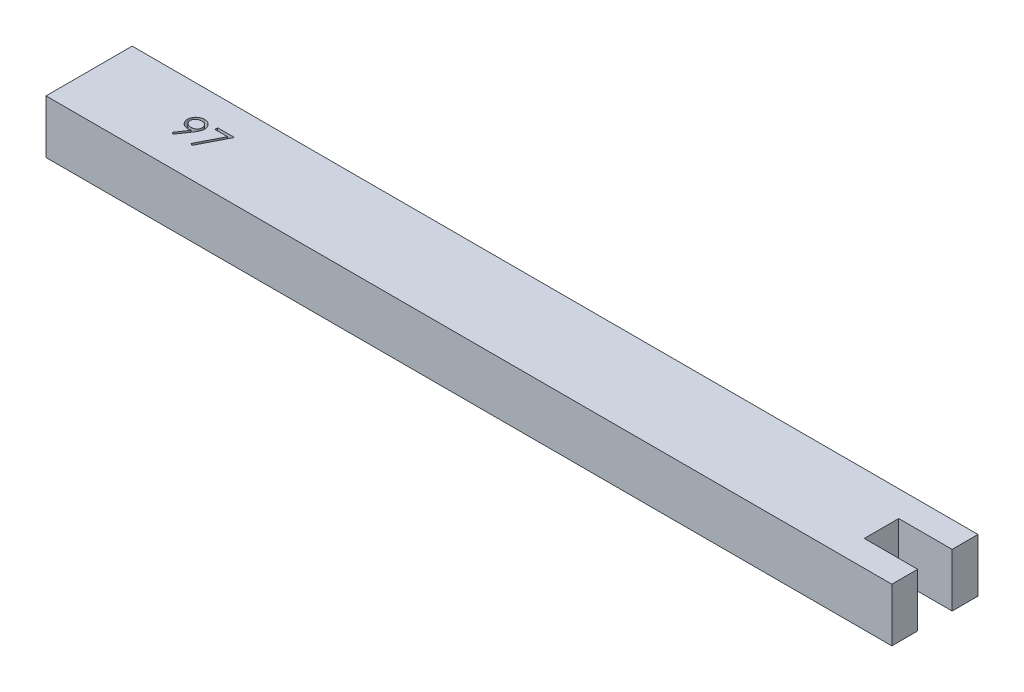
SolidWorks part; units mm, degrees
ref_plane "Front Plane" through (0, 0, 0) normal (0, 0, 1) x (1, 0, 0)
ref_plane "Top Plane" through (0, 0, 0) normal (0, 1, 0) x (1, 0, 0)
ref_plane "Right Plane" through (0, 0, 0) normal (1, 0, 0) x (0, 0, -1)
sketch "Sketch1" plane through (0, 0, 0) normal (0, 1, 0) x (1, 0, 0)
  line L0 (0, 0) -> (91.95, 0)
  line L2 (91.95, 10) -> (0, 10)
  line L3 (0, 10) -> (0, 0)
  line L4 (91.95, 10) -> (98.15, 10)
  line L5 (98.15, 10) -> (98.15, 7)
  line L6 (98.15, 7) -> (93.7123, 7)
  line L7 (93.7123, 7) -> (91.95, 7)
  line L8 (93.7123, 3) -> (98.15, 3)
  line L9 (98.15, 3) -> (98.15, 0)
  line L10 (98.15, 0) -> (91.95, 0)
  line L11 (93.7123, 3) -> (91.95, 3)
  line L13 (91.95, 3) -> (91.95, 7)
  dimension "D1" = 91.95
  dimension "D2" = 6.2
  dimension "D3" = 3
  dimension "D4" = 10
  dimension "D5" = 4
  dimension "D6" = 6.2
extrude "Boss-Extrude1" add sketch "Sketch1" along normal blind 6.2
sketch "Sketch2" plane through (0, 6.2, 0) normal (0, 1, 0) x (1, 0, 0)
  text T0 "97"
  point P1 (10.3962, 3.5787)
extrude "Cut-Extrude1" cut sketch "Sketch2" against normal blind 1
